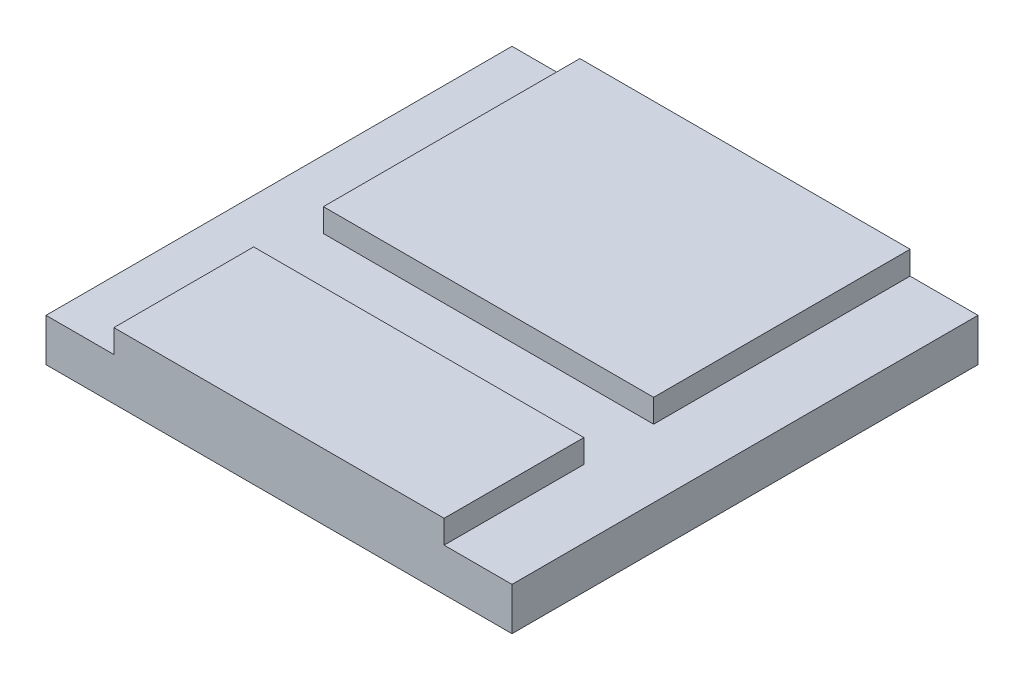
SolidWorks part; units mm, degrees
ref_plane "Front Plane" through (0, 0, 0) normal (0, 0, 1) x (1, 0, 0)
ref_plane "Top Plane" through (0, 0, 0) normal (0, 1, 0) x (1, 0, 0)
ref_plane "Right Plane" through (0, 0, 0) normal (1, 0, 0) x (0, 0, -1)
sketch "Sketch1" plane through (0, 0, 0) normal (0, 1, 0) x (1, 0, 0)
  line L1 (63.5, 63.5) -> (-63.5, 63.5)
  line L2 (63.5, 63.5) -> (63.5, -63.5)
  line L3 (63.5, -63.5) -> (-63.5, -63.5)
  line L4 (-63.5, 63.5) -> (-63.5, -63.5)
  line L5 (63.5, 63.5) -> (-63.5, -63.5) construction
  line L6 (63.5, -63.5) -> (-63.5, 63.5) construction
  point P0 (0, 0)
  dimension "D1" = 127
  dimension "D2" = 127
extrude "Boss-Extrude1" add sketch "Sketch1" along normal blind 18
sketch "Sketch2" plane through (0, 18, 0) normal (0, 1, 0) x (1, 0, 0)
  line L0 (-63.5, 63.5) -> (-63.5, -63.5) construction
  line L1 (-63.5, -25.4) -> (63.5, -25.4)
  line L2 (-63.5, -25.4) -> (-63.5, -6.4)
  line L3 (-63.5, -6.4) -> (63.5, -6.4)
  line L4 (63.5, -25.4) -> (63.5, -6.4)
  line L5 (63.5, -63.5) -> (63.5, 63.5) construction
  line L6 (-63.5, -63.5) -> (63.5, -63.5) construction
  dimension "D1" = 19
  dimension "D2" = 38.1
extrude "Cut-Extrude1" cut sketch "Sketch2" against normal blind 6.35
sketch "Sketch3" plane through (0, 18, 0) normal (0, 1, 0) x (1, 0, 0)
  line L0 (63.5, 63.5) -> (-63.5, 63.5) construction
  line L1 (63.5, -63.5) -> (45, -63.5)
  line L2 (63.5, -63.5) -> (63.5, 63.5)
  line L3 (63.5, 63.5) -> (45, 63.5)
  line L4 (45, -63.5) -> (45, 63.5)
  line L5 (-63.5, -63.5) -> (63.5, -63.5) construction
  line L6 (-63.5, 63.5) -> (-45, 63.5)
  line L7 (-63.5, 63.5) -> (-63.5, -63.5)
  line L8 (-63.5, -63.5) -> (-45, -63.5)
  line L9 (-45, 63.5) -> (-45, -63.5)
  dimension "D1" = 18.5
  dimension "D2" = 18.5
extrude "Cut-Extrude2" cut sketch "Sketch3" against normal blind 6.35
